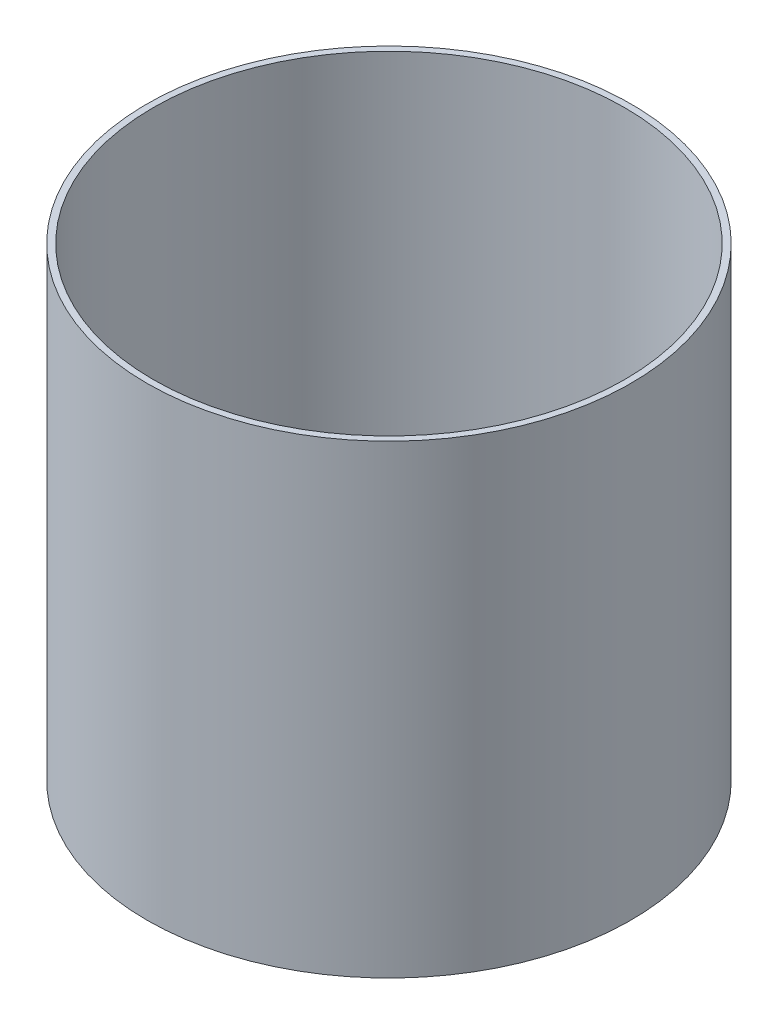
SolidWorks part; units mm, degrees
ref_plane "前视基准面" through (0, 0, 0) normal (0, 0, 1) x (1, 0, 0)
ref_plane "上视基准面" through (0, 0, 0) normal (0, 1, 0) x (1, 0, 0)
ref_plane "右视基准面" through (0, 0, 0) normal (1, 0, 0) x (0, 0, -1)
other "Configuration Table"
sketch "草图1" plane through (0, 0, 0) normal (0, 1, 0) x (1, 0, 0)
  circle A0 centre (0, 0) radius 19
  circle A1 centre (0, 0) radius 18.5
  dimension "D1" = 0.5
  dimension "D2" = 38
extrude "凸台-拉伸1" add sketch "草图1" along normal blind 36.5
